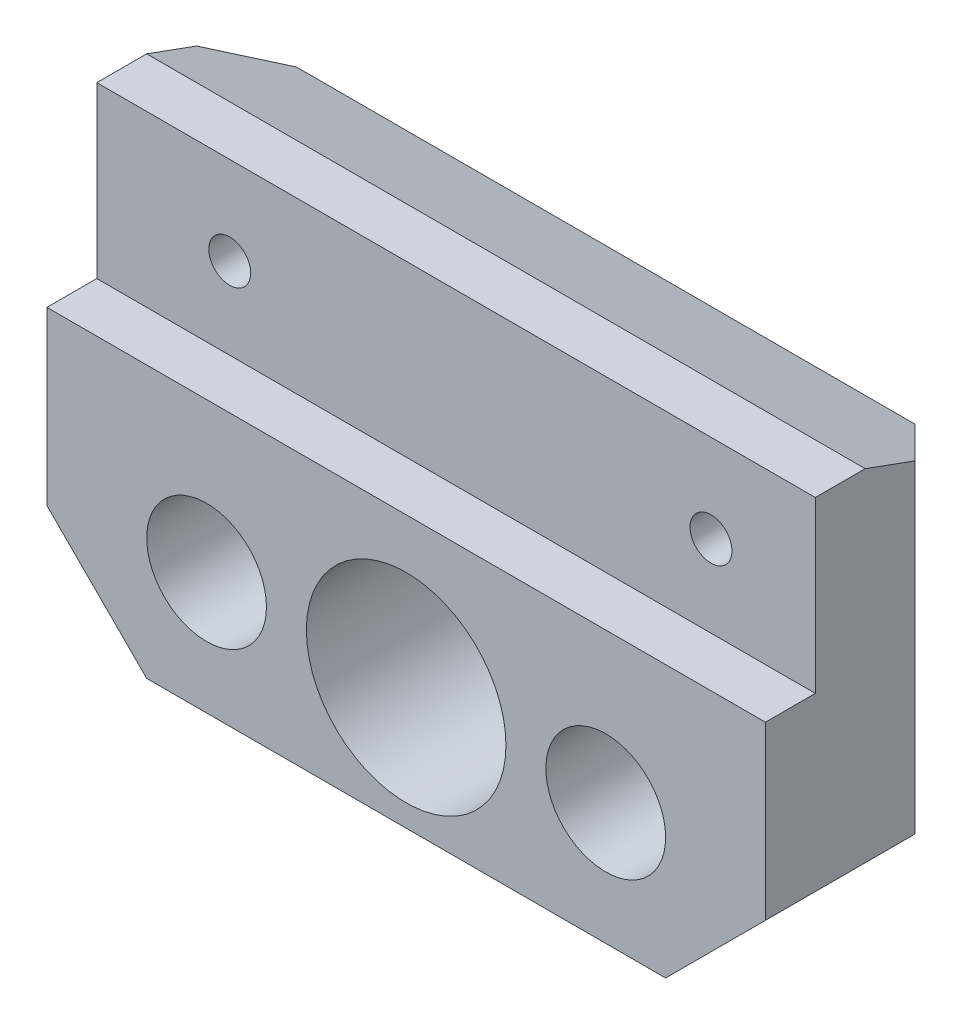
SolidWorks part; units mm, degrees
ref_plane "Ebene vorne" through (0, 0, 0) normal (0, 0, 1) x (1, 0, 0)
ref_plane "Ebene oben" through (0, 0, 0) normal (0, 1, 0) x (1, 0, 0)
ref_plane "Ebene rechts" through (0, 0, 0) normal (1, 0, 0) x (0, 0, -1)
sketch "Skizze1" plane through (0, 0, 0) normal (0, 0, 1) x (1, 0, 0)
  line L0 (0, 0) -> (107.9023, 0) construction
  line L1 (53.9613, 30.0276) -> (53.9613, -49.8276) construction
  line L3 (17.9613, 22.1) -> (89.9613, 22.1)
  line L4 (17.9613, 22.1) -> (17.9613, -22.1)
  line L5 (17.9613, -22.1) -> (89.9613, -22.1)
  line L6 (89.9613, 22.1) -> (89.9613, -22.1)
  circle A0 centre (53.9613, -9.9) radius 10
  circle A1 centre (33.9613, -9.9) radius 6
  circle A2 centre (73.9613, -9.9) radius 6
  dimension "D3" = 20
  dimension "D5" = 40
  dimension "D6" = 12
  dimension "D1" = 44.2
  dimension "D2" = 72
  dimension "D4" = 12.2
extrude "Aufsatz-Linear austragen1" add sketch "Skizze1" along normal blind 20
chamfer "Fase1" distance 10 angle 45 1 edges at (17.9613, -22.1, 10)
chamfer "Fase2" distance 10 angle 45 1 edges at (89.9613, -22.1, 10)
chamfer "Fase6" distance 10 angle 20 1 edges at (53.9613, 22.1, 0)
chamfer "Fase7" distance 5 angle 45 2 edges at (17.9613, 3.1801, 0) (89.9613, 3.1801, 0)
sketch "Skizze3" plane through (17.9613, 0, 0) normal (-1, 0, 0) x (0, 0, 1)
  line L0 (20, 22.1) -> (15, 22.1)
  line L1 (20, 22.1) -> (10, 22.1) construction
  line L2 (20, 22.1) -> (20, -12.1) construction
  line L3 (15, 22.1) -> (15, 5.1)
  line L4 (15, 5.1) -> (20, 5.1)
  line L5 (20, 5.1) -> (20, 22.1)
  dimension "D1" = 17
  dimension "D2" = 5
extrude "Schnitt-Linear austragen1" cut sketch "Skizze3" against normal blind 80
sketch "Skizze11" plane through (0, 0, 0) normal (0, 0, -1) x (-1, 0, 0)
  circle A0 centre (-53.9613, -9.9) radius 12
  dimension "D1" = 24
extrude "Schnitt-Linear austragen2" cut sketch "Skizze11" against normal blind 3.4 contours A0
sketch "Skizze12" [suppressed] plane through (0, 0, 15) normal (0, 0, 1) x (1, 0, 0)
sketch "Skizze13" [suppressed] plane through (0, 0, 15) normal (0, 0, 1) x (1, 0, 0)
  line L0 (17.9613, 22.1) -> (17.9613, 5.1) construction
  line L1 (89.9613, 22.1) -> (89.9613, 5.1) construction
  line L2 (53.9613, -28.9445) -> (53.9613, 31.7738) construction
  circle A0 centre (29.9613, 17.1813) radius 2.5
  circle A1 centre (77.9613, 17.1813) radius 2.5
  dimension "D1" = 5
  dimension "D2" = 48
hole_wizard "M5 Gewindebohrung1" positions "Skizze16" profile "Skizze17" tap size "M5" standard "DIN"
sketch "Skizze16" plane through (0, 0, 15) normal (0, 0, 1) x (1, 0, 0)
  point P0 (31.2827, 13.2732)
  point P2 (79.5056, 13.2732)
sketch "Skizze17" plane through (31.2827, 13.2732, 15) normal (1, 0, 0) x (0, -1, 0)
  line L0 (0, 0) -> (0, 13.2618)
  line L1 (0, 13.2618) -> (2.1, 12)
  line L2 (2.1, 12) -> (2.1, 0)
  line L5 (2.1, 0) -> (0, 0)
  line L10 (0, 13.2618) -> (-2.1, 12) construction
  line L11 (0, -6.35) -> (0, 107.95) construction
  dimension "Bohrerdurchmesser" = 4.2
  dimension "Bohrungstiefe" = 12
  dimension "Spitzenwinkel" = 118
cosmetic thread "Bohrungsgewinde3" parameters "D1"=8, "D2"=5
cosmetic thread "Bohrungsgewinde4" parameters "D1"=8, "D2"=5
